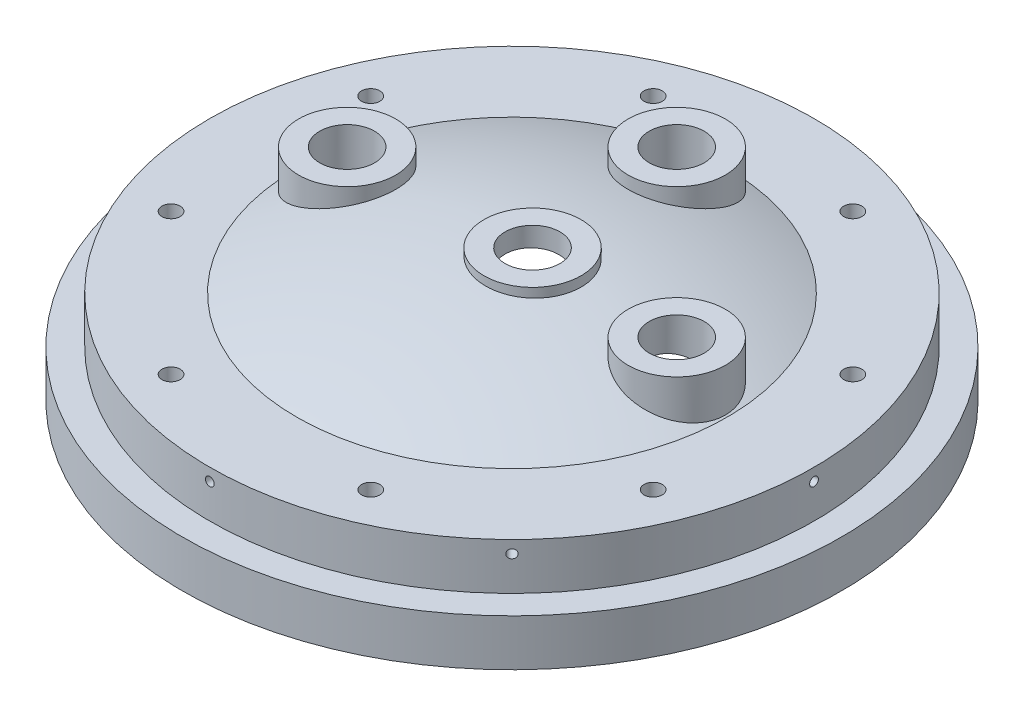
SolidWorks part; units mm, degrees
material "6061-T6"
ref_plane "Front Plane" through (0, 0, 0) normal (0, 0, 1) x (1, 0, 0)
ref_plane "Top Plane" through (0, 0, 0) normal (0, 1, 0) x (1, 0, 0)
ref_plane "Right Plane" through (0, 0, 0) normal (1, 0, 0) x (0, 0, -1)
sketch "Sketch1" plane through (0, 0, 0) normal (0, 0, 1) x (1, 0, 0)
  line L0 (146.05, 0) -> (152.4, 0)
  line L1 (152.4, 0) -> (152.4, 21.59)
  line L2 (152.4, 21.59) -> (139.7, 21.59)
  line L3 (139.7, 21.59) -> (139.7, 43.18)
  line L4 (0, 63.5) -> (0, 57.15)
  line L5 (146.05, 0) -> (146.05, 9.4998)
  line L6 (139.7, 43.18) -> (99.5473, 43.18)
  arc A0 (0, 63.5) -> (99.5473, 43.18) centre (0, -190.5) cw
  arc A1 (0, 57.15) -> (146.05, 9.4998) centre (0, -190.5) cw
  dimension "D1" = 152.4
  dimension "D2" = 6.35
  dimension "D7" = 247.65
  dimension "D3" = 12.7
  dimension "D4" = 21.59
  dimension "D5" = 43.18
  dimension "D6" = 6.35
  dimension "D8" = 63.5
revolve "Revolve1" add sketch "Sketch1" angle 360 about L4
ref_plane "Plane1" through (139.7, 0, 0) normal (1, 0, 0) x (0, 0, -1)
hole_wizard "Tap Drill for #10-32 Tap1" positions "Sketch4" profile "Sketch5" hole size "#10-32" standard "ANSI Inch"
sketch "Sketch4" plane through (139.7, 0, 0) normal (1, 0, 0) x (0, 0, -1)
  line L0 (152.4, 21.59) -> (-152.4, 21.59) construction
  point P0 (0, 37.465)
  dimension "D1" = 15.875
sketch "Sketch5" plane through (139.7, 37.465, 0) normal (0, 1, 0) x (0, 0, -1)
  line L0 (0, 0) -> (0, 11.3733)
  line L1 (0, 11.3733) -> (2.0193, 10.16)
  line L2 (2.0193, 10.16) -> (2.0193, 0)
  line L5 (2.0193, 0) -> (0, 0)
  line L10 (0, 11.3733) -> (-2.0193, 10.16) construction
  line L11 (0, -6.35) -> (0, 107.95) construction
  dimension "Hole Dia." = 4.0386
  dimension "Hole Depth" = 10.16
  dimension "Drill Angle" = 118
pattern_circular "CirPattern1" count 8 over 360 about axis through (0, 21.59, 0) along (0, 1, 0) of "Tap Drill for #10-32 Tap1"
ref_plane "Plane2" through (0, 63.5, 0) normal (0, 1, 0) x (1, 0, 0)
sketch "Sketch8" plane through (0, 63.5, 0) normal (0, 1, 0) x (1, 0, 0)
  line L0 (9.525, 0) -> (0, 0) construction
  circle A0 centre (9.525, 0) radius 22.479
  dimension "D1" = 44.958
  dimension "D2" = 9.525
extrude "Boss-Extrude1" add sketch "Sketch8" along normal blind 2.54 and the other way up to next
sketch "Sketch9" plane through (0, 63.5, 0) normal (0, 1, 0) x (1, 0, 0)
  line L0 (76.2, 0) -> (9.525, 0) construction
  circle A0 centre (76.2, 0) radius 22.479
  dimension "D1" = 76.2
  dimension "D2" = 44.958
extrude "Boss-Extrude2" add sketch "Sketch9" against normal up to next
hole_wizard "Hole1" positions "Sketch10" profile "Sketch12" legacy
sketch "Sketch10" plane through (0, 66.04, 0) normal (0, 1, 0) x (1, 0, 0)
  point P6 (9.525, 0)
sketch "Sketch12" plane through (9.525, 66.04, 0) normal (1, 0, 0) x (0, 0, 1)
  line L0 (0, 0) -> (0, 25.4)
  line L1 (0, 25.4) -> (12.7, 25.4)
  line L2 (12.7, 25.4) -> (12.7, 0)
  line L3 (12.7, 0) -> (0, 0)
  line L4 (0, 110) -> (0, -10) construction
  dimension "Diameter" = 25.4
  dimension "Depth" = 25.4
hole_wizard "Hole2" positions "Sketch14" profile "Sketch15" legacy
sketch "Sketch14" plane through (0, 63.5, 0) normal (0, 1, 0) x (1, 0, 0)
  point P0 (76.2, 0)
sketch "Sketch15" plane through (76.2, 63.5, 0) normal (1, 0, 0) x (0, 0, 1)
  line L0 (0, 0) -> (0, 25.4)
  line L1 (0, 25.4) -> (12.7, 25.4)
  line L2 (12.7, 25.4) -> (12.7, 0)
  line L3 (12.7, 0) -> (0, 0)
  line L4 (0, 110) -> (0, -10) construction
  dimension "Diameter" = 25.4
  dimension "Depth" = 25.4
pattern_circular "CirPattern2" count 3 every 90 about axis through (0, 0, 0) along (0, 1, 0) of "Hole2", "Boss-Extrude2"
hole_wizard "3/8-24 Tapped Hole1" positions "Sketch17" profile "Sketch19" tap size "3/8-24" standard "ANSI Inch"
sketch "Sketch17" plane through (0, 43.18, 0) normal (0, 1, 0) x (1, 0, 0)
  line L0 (111.4661, 46.1708) -> (0, 0)
  line L2 (0, 0) -> (139.7, 0)
  circle A0 centre (0, 0) radius 139.7 construction
  point P0 (111.4661, 46.1708)
  dimension "D1" = 22.5
  dimension "D2" = 120.65
sketch "Sketch19" plane through (111.4661, 43.18, -46.1708) normal (1, 0, 0) x (0, 0, 1)
  line L0 (0, 0) -> (0, 11.4235)
  line L1 (0, 11.4235) -> (4.2164, 8.89)
  line L2 (4.2164, 8.89) -> (4.2164, 0)
  line L5 (4.2164, 0) -> (0, 0)
  line L10 (0, 11.4235) -> (-4.2164, 8.89) construction
  line L11 (0, -6.35) -> (0, 107.95) construction
  dimension "Tap Drill Dia." = 8.4328
  dimension "Tap Drill Depth" = 8.89
  dimension "Drill Angle" = 118
cosmetic thread "Hole Thread1" parameters "D1"=8.89, "D2"=9.525
pattern_circular "CirPattern3" count 8 over 360 about axis through (0, 0, 0) along (0, 1, 0) of "3/8-24 Tapped Hole1"
